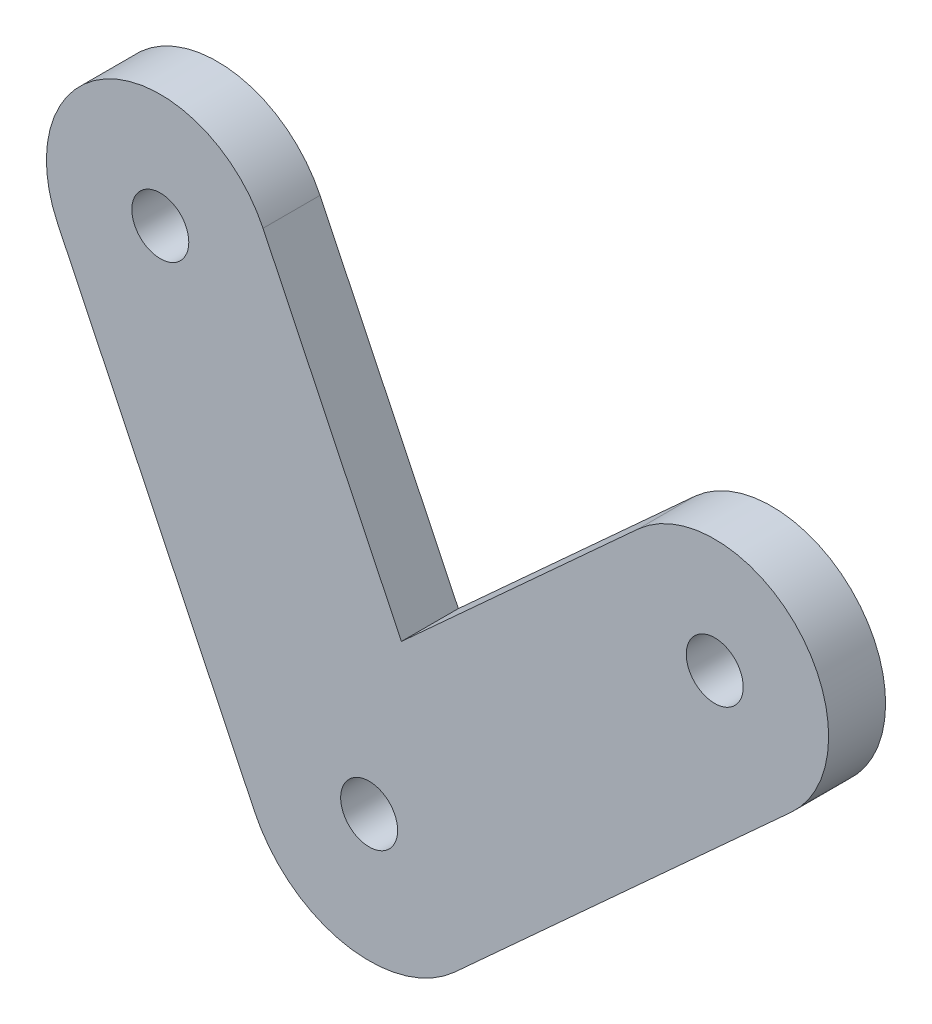
SolidWorks part; units mm, degrees
ref_plane "Front Plane" through (0, 0, 0) normal (0, 0, 1) x (1, 0, 0)
ref_plane "Top Plane" through (0, 0, 0) normal (0, 1, 0) x (1, 0, 0)
ref_plane "Right Plane" through (0, 0, 0) normal (1, 0, 0) x (0, 0, -1)
sketch "Sketch1" plane through (0, 0, 0) normal (0, 0, 1) x (1, 0, 0)
  line L0 (28.5131, 6.0601) -> (9.7481, -11.0422)
  line L1 (-1.4185, -8.8674) -> (-12.3937, 14.0271)
  line L3 (-0.9416, 19.5171) -> (6.7712, 3.4279)
  line L4 (6.7712, 3.4279) -> (19.9583, 15.4466)
  arc A0 (-1.4185, -8.8674) -> (9.7481, -11.0422) centre (4.9733, -5.8033) ccw
  arc A1 (-0.9416, 19.5171) -> (-12.3937, 14.0271) centre (-6.6677, 16.7721) ccw
  arc A2 (28.5131, 6.0601) -> (19.9583, 15.4466) centre (24.2357, 10.7533) ccw
  circle A3 centre (-6.6677, 16.7721) radius 1.5875
  circle A4 centre (24.2357, 10.7533) radius 1.5875
  circle A5 centre (4.9733, -5.8033) radius 1.5875
  point P9 (0, 0)
  point P14 (0, 0)
  dimension "D3" = 3.175
  dimension "D4" = 25.4
  dimension "D1" = 12.7
  dimension "D2" = 12.7
  dimension "D5" = 25.4
extrude "Boss-Extrude2" add sketch "Sketch1" along normal blind 3.175
